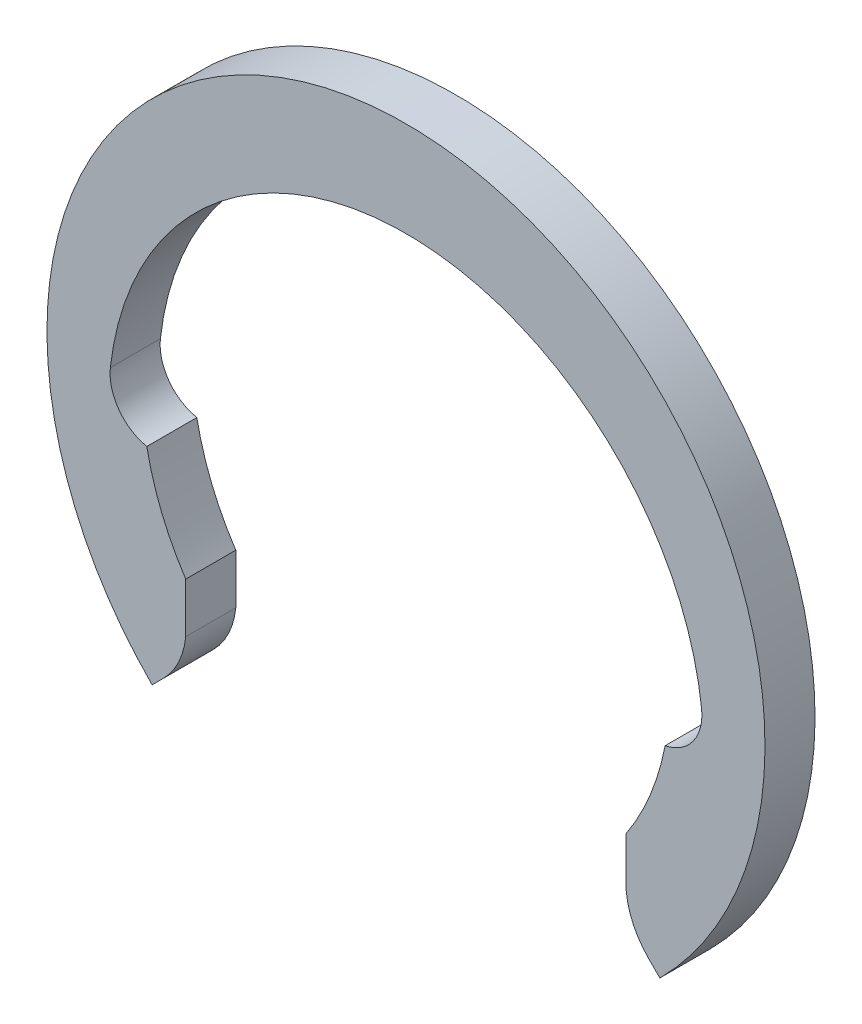
SolidWorks part; units mm, degrees
ref_plane "Front" through (0, 0, 0) normal (0, 0, 1) x (1, 0, 0)
ref_plane "Top" through (0, 0, 0) normal (0, 1, 0) x (1, 0, 0)
ref_plane "Right" through (0, 0, 0) normal (1, 0, 0) x (0, 0, -1)
sketch "Layout" plane through (0, 0, 0) normal (0, 0, 1) x (1, 0, 0)
  line L0 (0, 7.175) -> (0, -7.175) construction
  line L1 (-5.275, 0) -> (-5.9083, 0) construction
  line L2 (-7.175, 0) -> (-8.175, 0) construction
  line L3 (-5.275, 0) -> (5.275, 0) construction
  line L4 (-4.4017, -4.4017) -> (-4.4017, -2.9069) construction
  line L5 (-5.1793, -1) -> (5.1793, -1) construction
  line L6 (-5.275, 0) -> (-5.275, -1) construction
  line L7 (0, 0) -> (-3.73, -3.73) construction
  line L8 (-3.73, -3.73) -> (-5.0735, -5.0735) construction
  line L9 (-5.9083, 0) -> (-6.5417, 0) construction
  line L10 (-6.5417, 0) -> (-7.175, 0) construction
  circle A0 centre (0, 0) radius 7.175 construction
  circle A1 centre (0, 0) radius 5.275 construction
  arc A2 (0, 5.275) -> (-5.9083, 0) centre (0, -0.6714) ccw construction
  circle A3 centre (0, 0) radius 7.35 construction
  arc A4 (-5.9083, 0) -> (-5.1793, -1) centre (-4.9996, -0.1033) ccw construction
  dimension "D1" = 45
sketch "Sketch2" plane through (0, 0, 0) normal (0, 0, 1) x (1, 0, 0)
  line L0 (-4.4017, -4.4017) -> (-4.4017, -3.9035) construction
  line L1 (-4.4017, -3.9035) -> (-4.4017, -3.4052)
  line L2 (-4.4017, -3.4052) -> (-4.4017, -2.9069)
  line L4 (0, 7.175) -> (0, -7.175) construction
  line L5 (-4.4017, -4.4017) -> (-4.6257, -4.6257) construction
  line L6 (0, 7.175) -> (0, 5.275) construction
  line L7 (-4.6257, -4.6257) -> (-4.8496, -4.8496) construction
  line L8 (-4.8496, -4.8496) -> (-5.0735, -5.0735)
  line L9 (-3.73, -3.73) -> (-5.0735, -5.0735) construction
  line L10 (4.4017, -3.4052) -> (4.4017, -2.9069)
  line L11 (4.4017, -3.9035) -> (4.4017, -3.4052)
  line L12 (4.8496, -4.8496) -> (5.0735, -5.0735)
  circle A0 centre (0, 0) radius 7.175 construction
  arc A1 (0, 5.275) -> (-5.9083, 0) centre (0, -0.6714) ccw construction
  arc A2 (-5.9083, 0) -> (-5.1793, -1) centre (-4.9996, -0.1033) ccw construction
  circle A3 centre (0, 0) radius 5.275 construction
  arc A4 (5.0735, -5.0735) -> (-5.0735, -5.0735) centre (0, 0) ccw
  arc A5 (5.9083, 0) -> (-5.9083, 0) centre (0, -0.6714) ccw
  arc A6 (-5.9083, 0) -> (-5.1793, -1) centre (-4.9996, -0.1033) ccw
  arc A7 (-5.1793, -1) -> (-4.4017, -2.9069) centre (0, 0) ccw
  arc A8 (-4.4017, -3.9035) -> (-4.8496, -4.8496) centre (-5.949, -3.7501) cw
  arc A9 (4.4017, -3.9035) -> (4.8496, -4.8496) centre (5.949, -3.7501) ccw
  arc A10 (5.1793, -1) -> (4.4017, -2.9069) centre (0, 0) cw
  arc A11 (5.9083, 0) -> (5.1793, -1) centre (4.9996, -0.1033) cw
extrude "Boss-Extrude1" add sketch "Sketch2" along normal blind 1
equation "\"D1@Boss-Extrude1\"=\"thickness@Layout\""
